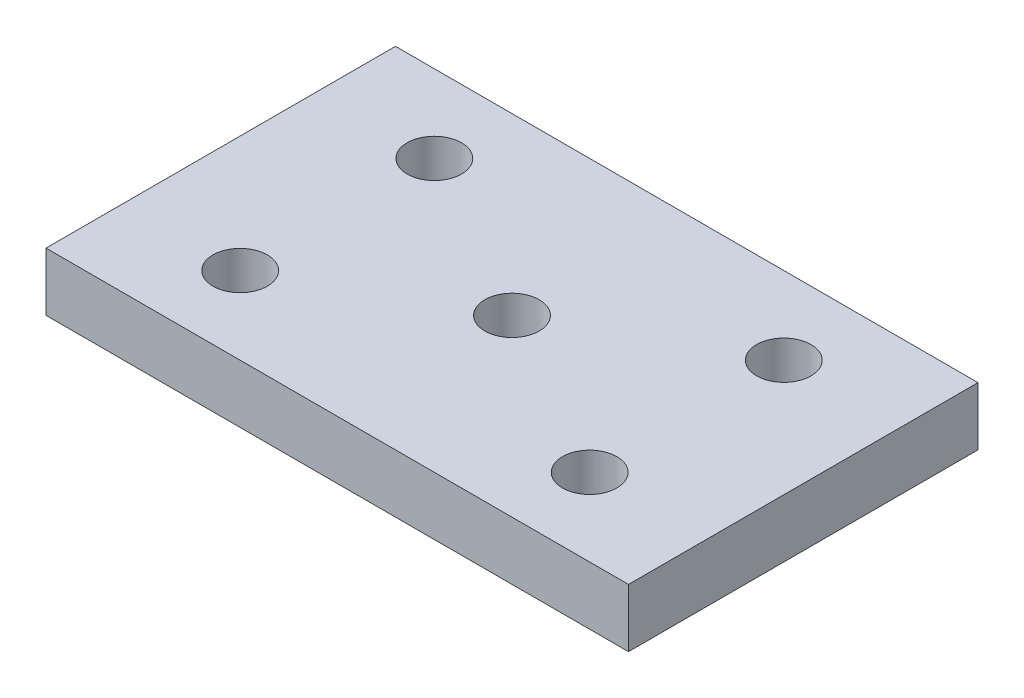
SolidWorks part; units mm, degrees
ref_plane "Front Plane" through (0, 0, 0) normal (0, 0, 1) x (1, 0, 0)
ref_plane "Top Plane" through (0, 0, 0) normal (0, 1, 0) x (1, 0, 0)
ref_plane "Right Plane" through (0, 0, 0) normal (1, 0, 0) x (0, 0, -1)
sketch "Sketch1" plane through (0, 0, 0) normal (0, 1, 0) x (1, 0, 0)
  line L0 (6, 4) -> (24, 4) construction
  line L1 (0, 0) -> (30, 0)
  line L2 (0, 0) -> (0, 18)
  line L3 (0, 18) -> (30, 18)
  line L4 (30, 0) -> (30, 18)
  line L5 (6, 14) -> (24, 14) construction
  line L6 (6, 14) -> (6, 4) construction
  circle A0 centre (6, 4) radius 1.4
  circle A1 centre (24, 4) radius 1.4
  circle A2 centre (24, 14) radius 1.4
  circle A3 centre (6, 14) radius 1.4
  circle A4 centre (15, 9) radius 1.4
  point P5 (15, 4)
  point P7 (15, 14)
  point P8 (15, 18)
  point P9 (15, 0)
  point P22 (6, 9)
  dimension "D3" = 2.8
  dimension "D9" = 2.8
  dimension "D1" = 18
  dimension "D2" = 30
  dimension "D6" = 18
  dimension "D7" = 4
  dimension "D8" = 10
  dimension "D4" = 2
  dimension "D5" = 2
extrude "Boss-Extrude1" add sketch "Sketch1" along normal blind 3
